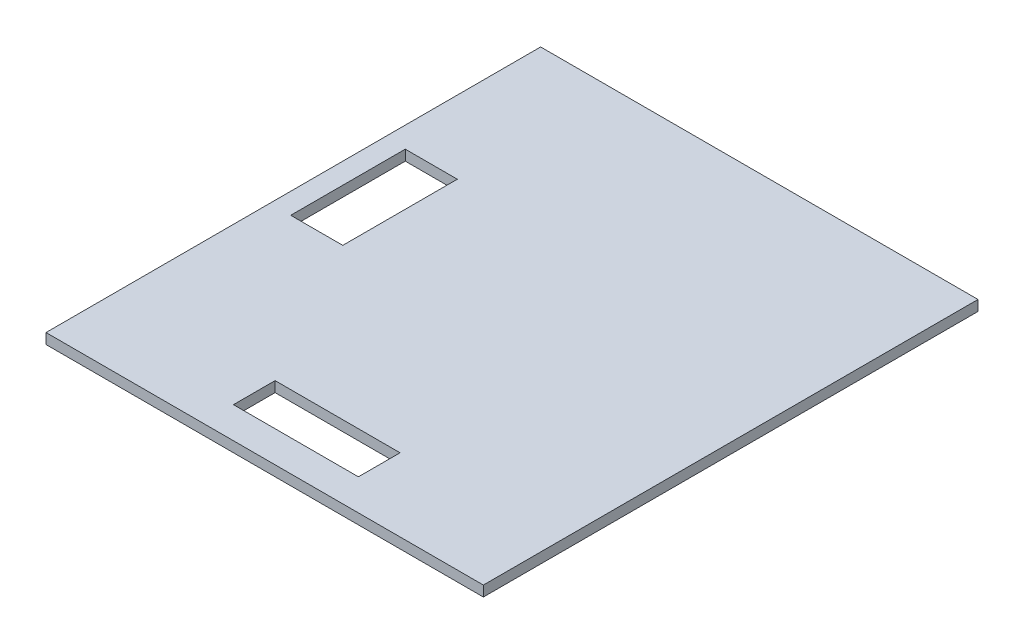
SolidWorks part; units mm, degrees
ref_plane "Front Plane" through (0, 0, 0) normal (0, 0, 1) x (1, 0, 0)
ref_plane "Top Plane" through (0, 0, 0) normal (0, 1, 0) x (1, 0, 0)
ref_plane "Right Plane" through (0, 0, 0) normal (1, 0, 0) x (0, 0, -1)
sketch "Sketch1" plane through (0, 0, 0) normal (0, 1, 0) x (1, 0, 0)
  line L1 (-21, -23.75) -> (21, -23.75)
  line L2 (-21, -23.75) -> (-21, 23.75)
  line L3 (-21, 23.75) -> (21, 23.75)
  line L4 (21, -23.75) -> (21, 23.75)
  line L5 (-21, -23.75) -> (21, 23.75) construction
  line L6 (-21, 23.75) -> (21, -23.75) construction
  point P0 (0, 0)
  dimension "D1" = 42
  dimension "D2" = 47.5
extrude "Boss-Extrude1" add sketch "Sketch1" along normal blind 1
sketch "Sketch2" plane through (0, 0, 0) normal (0, 1, 0) x (1, 0, 0)
  line L0 (0, 23.75) -> (39.6826, 23.75) construction
  line L1 (-19, 35.903) -> (-19, -31.5078) construction
  line L2 (8.6431, -23.75) -> (32.112, -23.75) construction
  line L3 (-14, 35.0952) -> (-14, -32.7644) construction
  line L4 (-21, -0.9148) -> (-21, -27.6642) construction
  line L5 (-6, 34.1976) -> (-6, -31.5078) construction
  line L6 (21, -4.3216) -> (21, -27.6011) construction
  line L7 (6, 32.7614) -> (6, -32.7644) construction
  line L8 (-34.3831, 8.75) -> (43.1524, 8.75) construction
  line L9 (-31.7334, -2.25) -> (39.9349, -2.25) construction
  line L10 (34.3831, -16.75) -> (-37.7268, -16.75) construction
  line L11 (-38.6732, -20.75) -> (42.7739, -20.75) construction
  line L13 (-19, -2.25) -> (-14, -2.25)
  line L14 (-19, -2.25) -> (-19, 8.75)
  line L15 (-19, 8.75) -> (-14, 8.75)
  line L16 (-14, -2.25) -> (-14, 8.75)
  line L17 (-6, -20.75) -> (6, -20.75)
  line L18 (-6, -20.75) -> (-6, -16.75)
  line L19 (-6, -16.75) -> (6, -16.75)
  line L20 (6, -20.75) -> (6, -16.75)
  point P17 (-6, -16.75)
  point P25 (6, -16.75)
  point P26 (6, -20.75)
  point P27 (-6, -20.75)
  point P28 (-19, 8.75)
  point P29 (-14, 8.75)
  point P30 (-14, -2.25)
  point P31 (-19, -2.25)
  dimension "D1" = 3
  dimension "D2" = 7
  dimension "D3" = 26
  dimension "D4" = 15
  dimension "D5" = 2
  dimension "D6" = 7
  dimension "D7" = 15
  dimension "D8" = 15
extrude "Cut-Extrude1" cut sketch "Sketch2" along normal blind 5
